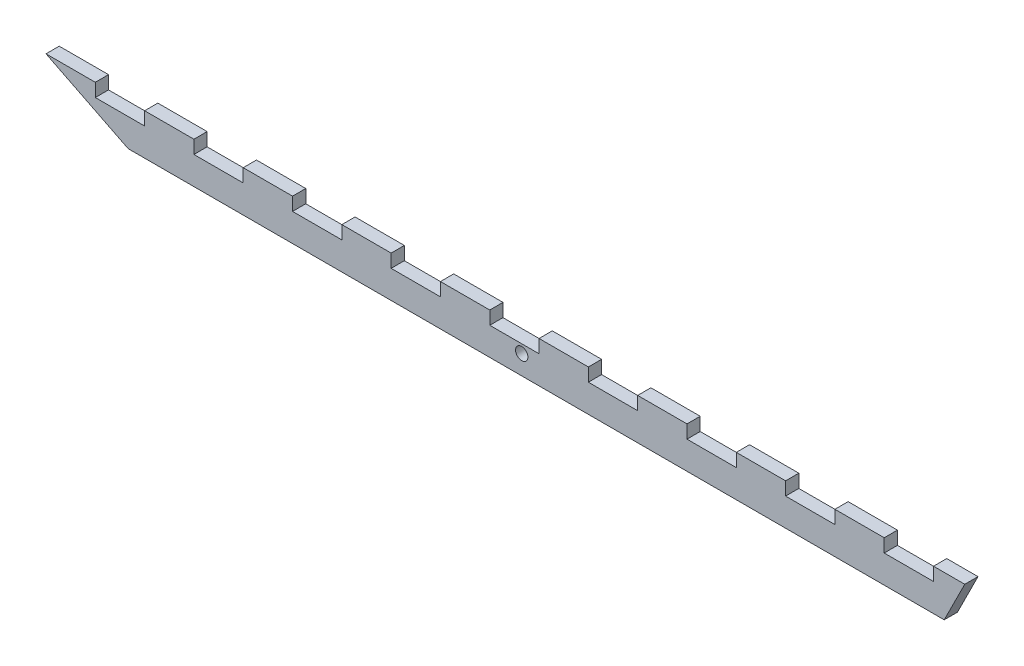
SolidWorks part; units mm, degrees
ref_plane "Front Plane" through (0, 0, 0) normal (0, 0, 1) x (1, 0, 0)
ref_plane "Top Plane" through (0, 0, 0) normal (0, 1, 0) x (1, 0, 0)
ref_plane "Right Plane" through (0, 0, 0) normal (1, 0, 0) x (0, 0, -1)
sketch "Sketch1" plane through (0, 0, 0) normal (0, 0, 1) x (1, 0, 0)
  line L0 (-95.7754, -4.7039) -> (-115.7754, 5.2961)
  line L3 (-95.7754, -4.7039) -> (102.8314, -4.7039)
  line L5 (-115.7754, 5.2961) -> (107.8314, 5.2961)
  line L6 (-95.7754, -4.7039) -> (107.8314, 5.2961) construction
  line L7 (102.8314, -4.7039) -> (107.8314, 5.2961)
  line L8 (102.8314, -4.7039) -> (-115.7754, 5.2961) construction
  circle A0 centre (0, 0) radius 1.5
  dimension "D5" = 3
  dimension "D1" = 26.565
  dimension "D2" = 223.6068
  dimension "D3" = 10
  dimension "D4" = 63.435
extrude "Boss-Extrude1" add sketch "Sketch1" along normal mid plane 3.22
sketch "Sketch2" plane through (0, 0, 1.61) normal (0, 0, 1) x (1, 0, 0)
  line L0 (107.8314, 5.2961) -> (-115.7754, 5.2961) construction
  line L1 (-103.7754, 5.2961) -> (-91.7754, 5.2961)
  line L2 (-103.7754, 5.2961) -> (-103.7754, 2.0761)
  line L3 (-103.7754, 2.0761) -> (-91.7754, 2.0761)
  line L4 (-91.7754, 5.2961) -> (-91.7754, 2.0761)
  line L5 (-115.7754, 5.2961) -> (-103.7754, 5.2961) construction
  dimension "D1" = 12
  dimension "D2" = 3.22
extrude "Cut-Extrude1" cut sketch "Sketch2" against normal up to next (3.22 mm away)
pattern_linear "LPattern1" count 9 spacing 24 along (1, 0, 0) of "Cut-Extrude1"
equation "\"D1@Sketch1\"=atn(10/20)"
equation "\"D2@Sketch1\"=sqr(100^2+200^2)"
equation "\"D4@Sketch1\"=90-\"D1@Sketch1\""
equation "\"D3@LPattern1\"=2*\"D1@Sketch2\""
